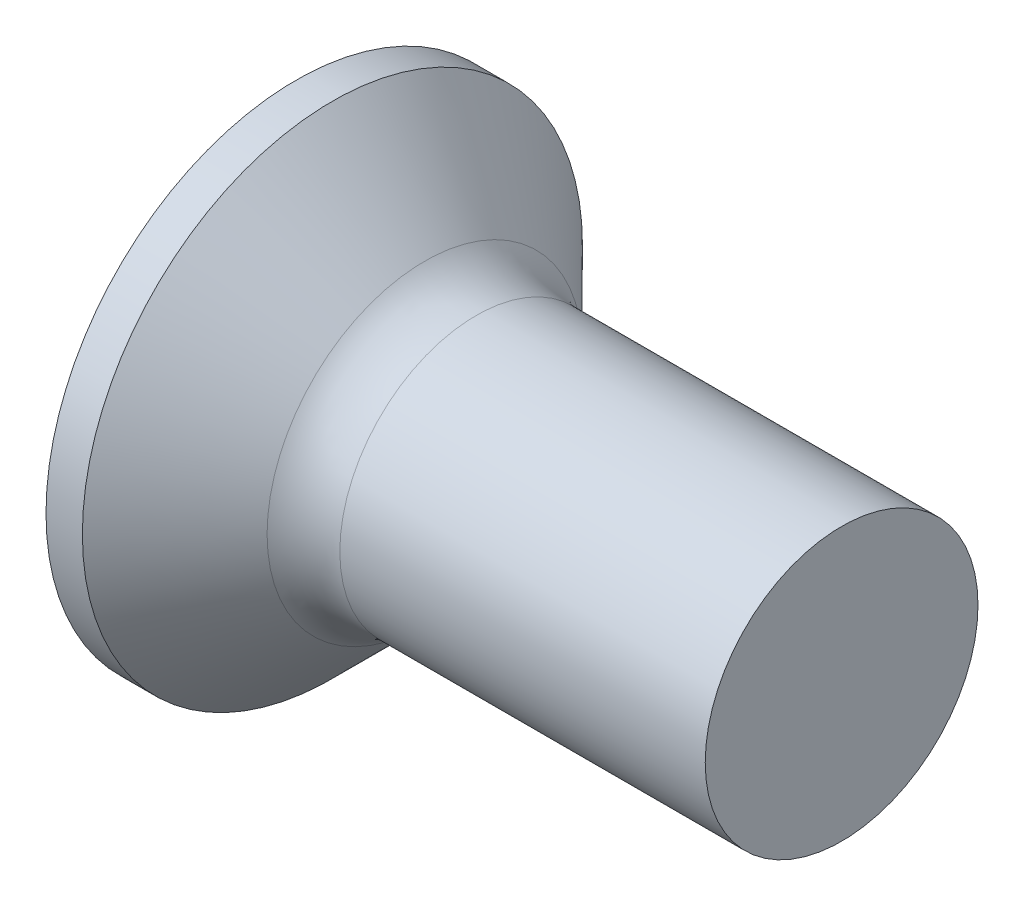
SolidWorks part; units mm, degrees
ref_plane "Plane1" through (0, 0, 0) normal (0, 0, 1) x (1, 0, 0)
ref_plane "Plane2" through (0, 0, 0) normal (0, 1, 0) x (1, 0, 0)
ref_plane "Plane3" through (0, 0, 0) normal (1, 0, 0) x (0, 0, -1)
sketch "BodySke" plane through (0, 0, 0) normal (0, 0, 1) x (1, 0, 0)
  line L0 (0, 0) -> (0, 2.75)
  line L1 (0, 2.75) -> (0.4, 2.75)
  line L2 (1.65, 1.5) -> (6, 1.5)
  line L3 (6, 1.5) -> (6, 0)
  line L4 (6, 0) -> (0, 0)
  line L5 (-6.35, 0) -> (82.55, 0) construction
  line L6 (1.65, -1.5) -> (6, -1.5) construction
  line L7 (0.4, -2.75) -> (1.65, -1.5) construction
  line L8 (0.4, 2.75) -> (1.65, 1.5)
  line L9 (0, -2.75) -> (0.4, -2.75) construction
  line L10 (2.15, 3.0875) -> (2.15, -6.4375) construction
  line L11 (0, 6.35) -> (0, -3.175) construction
  dimension "Diameter" = 3
  dimension "Length" = 6
  dimension "Head_ht" = 1.65
  dimension "Head_dia" = 5.5
  dimension "Head_ang" = 90
  dimension "D6" = 0.4
  dimension "Advance" = 0.5
  dimension "Thread_nom" = 6
revolve "Base-Revolve" add sketch "BodySke"
cosmetic thread "ThreadCosmetic"
fillet "Fillet1" radius 0.8 1 edges at (1.65, 0, 1.5)
sketch "Sketch3" plane through (0, 0, 0) normal (-1, 0, 0) x (0, 0, 1)
  line L0 (-0.37, 1.5) -> (0.37, 1.5)
  line L1 (0.37, 1.5) -> (0.37, -1.5)
  line L2 (0.37, -1.5) -> (-0.37, -1.5)
  line L3 (-0.37, -1.5) -> (-0.37, 1.5)
  dimension "D1" = 1.5
  dimension "Cross_dia" = 3
  dimension "D2" = 0.37
  dimension "Cross_width" = 0.74
ref_plane "Plane4" through (2.01, 0, 0) normal (-1, 0, 0) x (0, 0, 1)
sketch "Sketch4" plane through (2.01, 0, 0) normal (-1, 0, 0) x (0, 0, 1)
  line L0 (-0.37, 0.4979) -> (0.37, 0.4979)
  line L3 (0.37, 0.4979) -> (0.37, -0.4979)
  line L4 (0.37, -0.4979) -> (-0.37, -0.4979)
  line L5 (-0.37, -0.4979) -> (-0.37, 0.4979)
  dimension "D1" = 0.74
  dimension "D2" = 0.9957
  dimension "D3" = 0.37
  dimension "D4" = 0.4979
loft "Recess" cut profiles "Sketch3", "Sketch4"
pattern_circular "RecPat" count 2 every 90 about axis through (0, 0, 0) along (1, 0, 0) of "Recess"
sketch "RecCorSke" plane through (0, 0, 0) normal (0, 0, 1) x (1, 0, 0)
  line L0 (-3.175, 0) -> (15.875, 0) construction
  line L2 (0, 0) -> (0, 0.6966)
  line L3 (0, 0.6966) -> (2.01, 0.556)
  line L4 (2.01, 0.556) -> (2.1907, 0)
  line L5 (2.1907, 0) -> (0, 0)
  dimension "Diameter" = 1.112
  dimension "Depth" = 2.01
  dimension "Draft_angle" = 4
  dimension "Bottom_angle" = 18
revolve "RecessCore" cut sketch "RecCorSke" angle 360 about L0
sketch "ThdSchSke" plane through (0, 0, 0) normal (0, 0, 1) x (1, 0, 0)
  line L0 (2.15, -1.2195) -> (1.9536, -1.5)
  line L1 (2.15, -1.2195) -> (2.3464, -1.5)
  line L2 (2.3464, -1.5) -> (2.3464, -1.875)
  line L3 (-3.175, 0) -> (5.1513, 0) construction
  line L5 (2.3464, -1.875) -> (1.9536, -1.875)
  line L6 (1.9536, -1.875) -> (1.9536, -1.5)
  line L7 (0, 2.75) -> (0, -2.75) construction
  dimension "Thread_minor" = 2.439
  dimension "Diameter" = 3
  dimension "Start" = 2.15
  dimension "SideAngle" = 55
  dimension "VeeAngle" = 70
  dimension "Overcut" = 3.75
revolve "ThreadSchematic" [suppressed] cut sketch "ThdSchSke" angle 360 about L3
pattern_linear "ThdSchPat" [suppressed]
equation "\"D1@Sketch3\" = \"Cross_dia@Sketch3\" / 2"
equation "\"D2@Sketch3\" = \"Cross_width@Sketch3\" / 2"
equation "\"Depth@RecCorSke\" = \"Cross_depth@Plane4\""
equation "\"D1@Sketch4\" = \"Cross_width@Sketch3\""
equation "\"D2@Sketch4\" = \"Cross_dia@Sketch3\" - 2.0 * \"Cross_depth@Plane4\" * tan(26.5  * 0.017453292)"
equation "\"D3@Sketch4\" = \"D1@Sketch4\" / 2"
equation "\"D4@Sketch4\" = \"D2@Sketch4\" / 2"
equation "\"Thread_length@ThreadCosmetic\" = ((sgn( (\"Length@BodySke\" - \"Advance@BodySke\" * 1.0 - \"Head_ht@BodySke\" ) - \"Thread_nom@BodySke\" )-1)*( (\"Length@BodySke\" - \"Advance@BodySke\" * 1.0 - \"Head_ht@BodySke\" ) - \"Thread_nom@BodySke\" ))/-2+ \"Thread_nom@BodySke\""
equation "\"Thread_minor@ThdSchSke\" = \"Thread_minor@ThreadCosmetic\""
equation "\"Diameter@ThdSchSke\" = \"Diameter@BodySke\""
equation "\"Overcut@ThdSchSke\" = \"Diameter@BodySke\" * 1.25"
equation "\"Start@ThdSchSke\" = 0.000001 + \"Length@BodySke\" - \"Thread_length@ThreadCosmetic\"  '---Countersunk---"
equation "\"Num_threads@ThdSchPat\" = int( \"Thread_length@ThreadCosmetic\" / \"Advance@BodySke\" + 0.999 )  + 1"
equation "\"Advance@ThdSchPat\" = \"Thread_length@ThreadCosmetic\" /  (\"Num_threads@ThdSchPat\" - 1) 'relax it"
